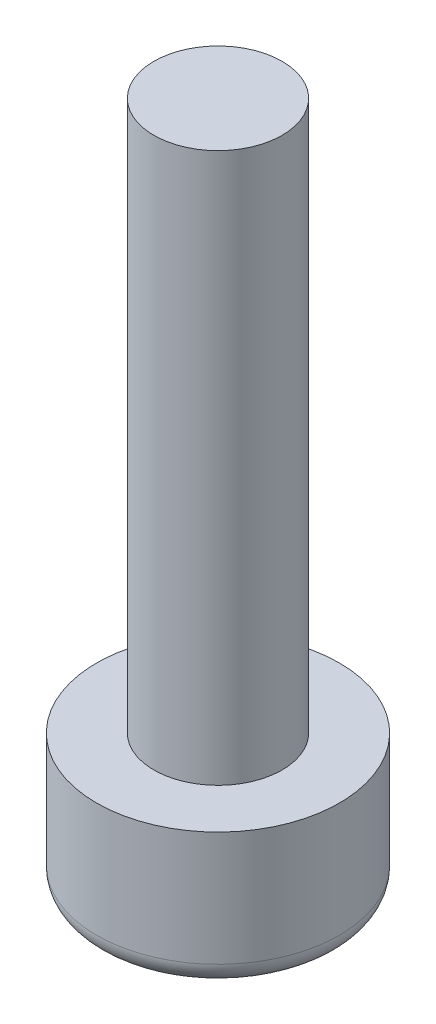
SolidWorks part; units mm, degrees
ref_plane "Front Plane" through (0, 0, 0) normal (0, 0, 1) x (1, 0, 0)
ref_plane "Top Plane" through (0, 0, 0) normal (0, 1, 0) x (1, 0, 0)
ref_plane "Right Plane" through (0, 0, 0) normal (1, 0, 0) x (0, 0, -1)
sketch "Sketch2" plane through (0, 0, 0) normal (0, 0, 1) x (1, 0, 0)
  line L0 (0, 0) -> (0, 25) construction
  line L7 (0, 0) -> (2.65, 0)
  line L8 (2.65, 0) -> (2.65, 3)
  line L9 (2.65, 3) -> (1.4, 3)
  line L10 (1.4, 3) -> (1.4, 15)
  line L11 (1.4, 15) -> (0, 15)
  line L12 (0, 15) -> (0, 0)
  dimension "D1" = 2.65
  dimension "D2" = 1.4
  dimension "D3" = 3
  dimension "D4" = 12
  dimension "D5" = 25
revolve "Revolve1" add sketch "Sketch2" angle 360 about L0
sketch "Sketch3" plane through (0, 0, 0) normal (0, -1, 0) x (1, 0, 0)
  line L1 (-1.4434, 0) -> (-0.7217, -1.25)
  line L2 (-0.7217, -1.25) -> (0.7217, -1.25)
  line L3 (0.7217, -1.25) -> (1.4434, 0)
  line L4 (1.4434, 0) -> (0.7217, 1.25)
  line L5 (0.7217, 1.25) -> (-0.7217, 1.25)
  line L6 (-0.7217, 1.25) -> (-1.4434, 0)
  circle A0 centre (0, 0) radius 1.25 construction
  dimension "D1" = 2.5
extrude "Cut-Extrude1" cut sketch "Sketch3" against normal blind 2
sketch "Sketch5" plane through (0, 0, 0) normal (0, -1, 0) x (1, 0, 0)
  circle A0 centre (0, 0) radius 1.75
  dimension "D1" = 3.5
ref_plane "Plane1" through (0, 0, 0) normal (0, 0, -1) x (-1, 0, 0)
sketch "Sketch6" plane through (0, 0, 0) normal (0, 0, -1) x (-1, 0, 0)
  line L0 (0, 0) -> (0, 0.3)
  line L1 (0, 0) -> (-1.75, 0)
  line L2 (-1.75, 0) -> (1.75, 0) construction
  line L3 (0, 0.3) -> (1, 0.3) construction
  arc A0 (-1.75, 0) -> (0, 0.3) centre (0, -4.9542) cw
  dimension "D1" = 1
  dimension "D2" = 0.3
revolve "Cut-Revolve1" cut sketch "Sketch6" angle 360 about L0
fillet "Fillet1" radius 0.5 1 edges at (0, 0, -2.65)
